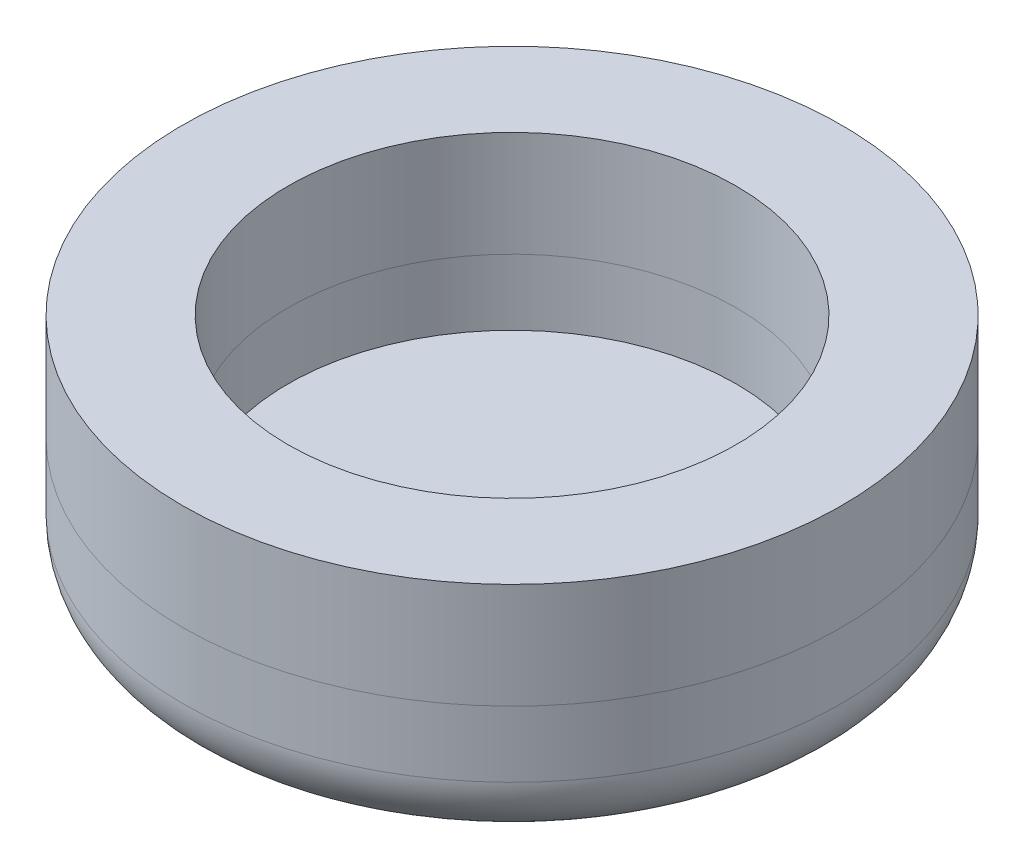
SolidWorks part; units mm, degrees
ref_plane "Front Plane" through (0, 0, 0) normal (0, 0, 1) x (1, 0, 0)
ref_plane "Top Plane" through (0, 0, 0) normal (0, 1, 0) x (1, 0, 0)
ref_plane "Right Plane" through (0, 0, 0) normal (1, 0, 0) x (0, 0, -1)
sketch "Sketch1" plane through (0, 0, 0) normal (0, 1, 0) x (1, 0, 0)
  circle A0 centre (0, 0) radius 6.35
  dimension "D1" = 12.7
extrude "Boss-Extrude1" add sketch "Sketch1" along normal blind 2.54
sketch "Sketch2" plane through (0, 2.54, 0) normal (0, 1, 0) x (1, 0, 0)
  circle A0 centre (0, 0) radius 3.429
  dimension "D1" = 6.858
fillet "Fillet2" radius 1.27 1 edges at (0, 0, 6.35)
extrude "Cut-Extrude2" cut sketch "Sketch2" against normal blind 1.27
sketch "Sketch3" plane through (0, 2.54, 0) normal (0, 1, 0) x (1, 0, 0)
  circle A0 centre (0, 0) radius 6.35
  circle A1 centre (0, 0) radius 3.429
extrude "Boss-Extrude2" add sketch "Sketch3" along normal blind 2.032 separate body
sketch "Sketch4" plane through (0, 1.27, 0) normal (0, 1, 0) x (1, 0, 0)
  circle A0 centre (0, 0) radius 3.9688
  dimension "D1" = 7.9375
extrude "Cut-Extrude3" cut sketch "Sketch4" along normal up to surface (3.302 mm away) up to face at (0, 4.572, 6.35)
sketch "Sketch5" plane through (0, 4.572, 0) normal (0, 1, 0) x (1, 0, 0)
  circle A0 centre (0, 0) radius 4.318
extrude "Cut-Extrude4" cut sketch "Sketch5" against normal up to surface (3.302 mm away)
